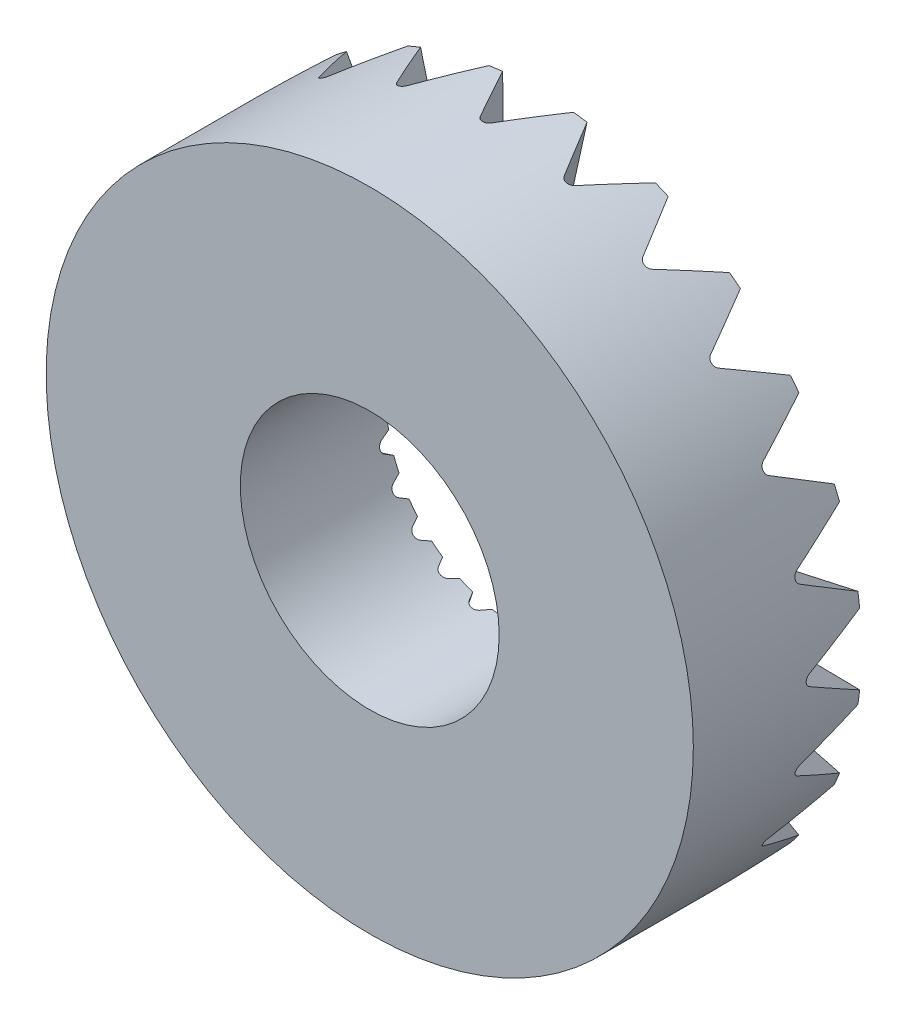
SolidWorks part; units mm, degrees
ref_plane "Vorne" through (0, 0, 0) normal (0, 0, 1) x (1, 0, 0)
ref_plane "Oben" through (0, 0, 0) normal (0, 1, 0) x (1, 0, 0)
ref_plane "Rechts" through (0, 0, 0) normal (1, 0, 0) x (0, 0, -1)
sketch "Skizze1" plane through (0, 0, 0) normal (1, 0, 0) x (0, 0, -1)
  line L0 (0, 0) -> (78.6332, 0) construction
  line L1 (0, 10) -> (0, 25)
  line L2 (0, 25) -> (13, 25)
  line L3 (13, 25) -> (11.2856, 10)
  line L4 (11.2856, 10) -> (0, 10)
  dimension "D1" = 20
  dimension "D2" = 50
  dimension "D3" = 13
  dimension "D4" = 83.48
revolve "Rotation1" add sketch "Skizze1" angle 360 about L0
sketch "Skizze2" plane through (0, 0, 0) normal (1, 0, 0) x (0, 0, -1)
  line L0 (6.5, 25) -> (6.5, -25) construction
  line L1 (13, 25) -> (0, 25) construction
  line L2 (0, -25) -> (13, -25) construction
ref_plane "Ebene1" through (-0.7333, 0, -0.0838) normal (0.9935, 0, 0.1136) x (0.1136, 0, -0.9935)
sketch "Skizze3" plane through (-0.7333, 0, -0.0838) normal (0.9935, 0, 0.1136) x (0.1136, 0, -0.9935)
  line L0 (0, 0) -> (19.6603, 0) construction
  line L1 (19.6603, 5) -> (19.6603, -5)
  line L2 (19.6603, 5) -> (11.75, 0.433)
  line L3 (11.75, -0.433) -> (19.6603, -5)
  arc A0 (11.75, 0.433) -> (11.75, -0.433) centre (12, 0) ccw
  dimension "D2" = 0.5
  dimension "D1" = 60
  dimension "D3" = 10
  dimension "D4" = 12
extrude "Schnitt-Linear austragen1" cut sketch "Skizze3" along normal through all
pattern_circular "Kreismuster1" count 24 over 360 about axis through (0, 0, 0) along (0, 0, 1) of "Schnitt-Linear austragen1"
